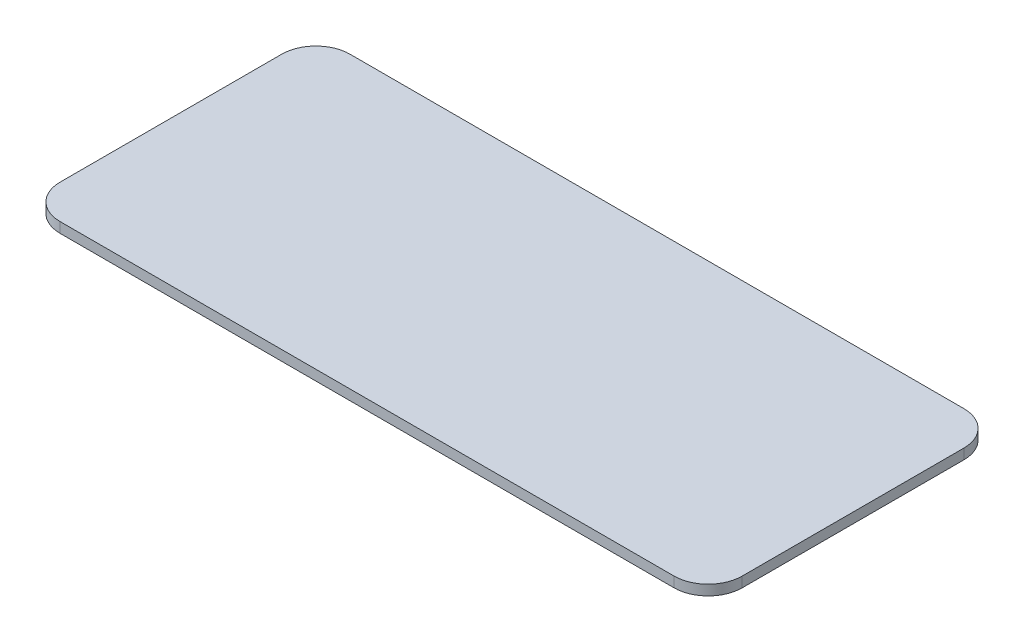
SolidWorks part; units mm, degrees
ref_plane "Front Plane" through (0, 0, 0) normal (0, 0, 1) x (1, 0, 0)
ref_plane "Top Plane" through (0, 0, 0) normal (0, 1, 0) x (1, 0, 0)
ref_plane "Right Plane" through (0, 0, 0) normal (1, 0, 0) x (0, 0, -1)
sketch "Sketch1" plane through (0, 0, 0) normal (0, 1, 0) x (1, 0, 0)
  line L1 (-90, 42.5) -> (90, 42.5)
  line L2 (-100, 32.5) -> (-100, -32.5)
  line L3 (-90, -42.5) -> (90, -42.5)
  line L4 (100, 32.5) -> (100, -32.5)
  line L5 (-100, 42.5) -> (100, -42.5) construction
  line L6 (-100, -42.5) -> (100, 42.5) construction
  arc A0 (-100, -32.5) -> (-90, -42.5) centre (-90, -32.5) ccw
  arc A1 (90, -42.5) -> (100, -32.5) centre (90, -32.5) ccw
  arc A2 (100, 32.5) -> (90, 42.5) centre (90, 32.5) ccw
  arc A3 (-90, 42.5) -> (-100, 32.5) centre (-90, 32.5) ccw
  point P0 (0, 0)
  dimension "D3" = 10
  dimension "D1" = 85
  dimension "D2" = 200
extrude "Boss-Extrude2" add sketch "Sketch1" along normal blind 3
